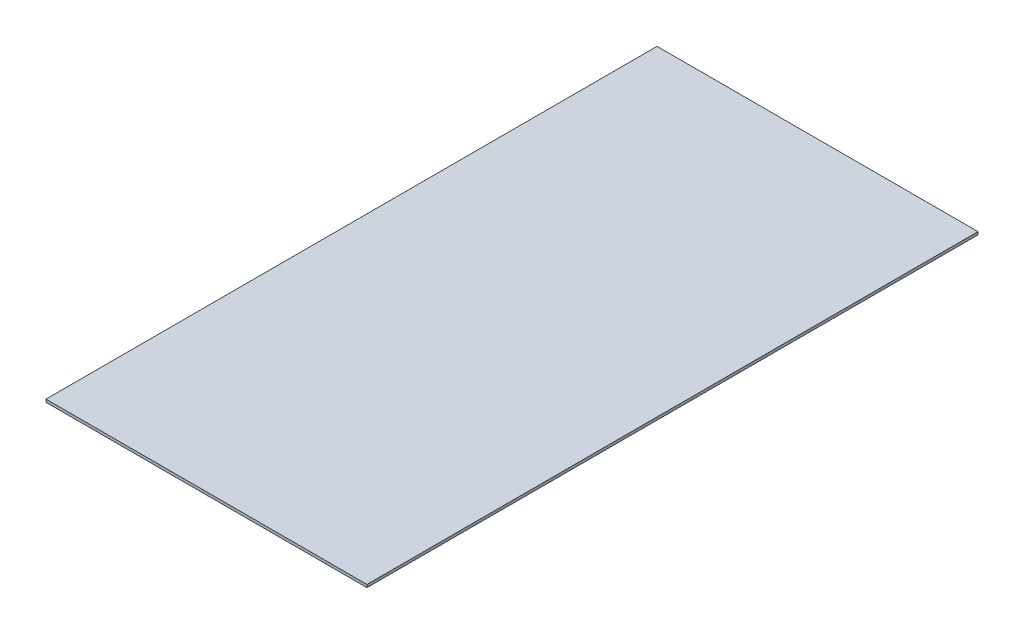
SolidWorks part; units mm, degrees
ref_plane "前视基准面" through (0, 0, 0) normal (0, 0, 1) x (1, 0, 0)
ref_plane "上视基准面" through (0, 0, 0) normal (0, 1, 0) x (1, 0, 0)
ref_plane "右视基准面" through (0, 0, 0) normal (1, 0, 0) x (0, 0, -1)
sketch "草图1" plane through (0, 0, 0) normal (0, 1, 0) x (1, 0, 0)
  line L1 (-114.5, -218) -> (114.5, -218)
  line L2 (-114.5, -218) -> (-114.5, 218)
  line L3 (-114.5, 218) -> (114.5, 218)
  line L4 (114.5, -218) -> (114.5, 218)
  line L5 (-114.5, -218) -> (114.5, 218) construction
  line L6 (-114.5, 218) -> (114.5, -218) construction
  point P0 (0, 0)
  dimension "D1" = 229
  dimension "D2" = 436
extrude "凸台-拉伸1" add sketch "草图1" along normal blind 2
